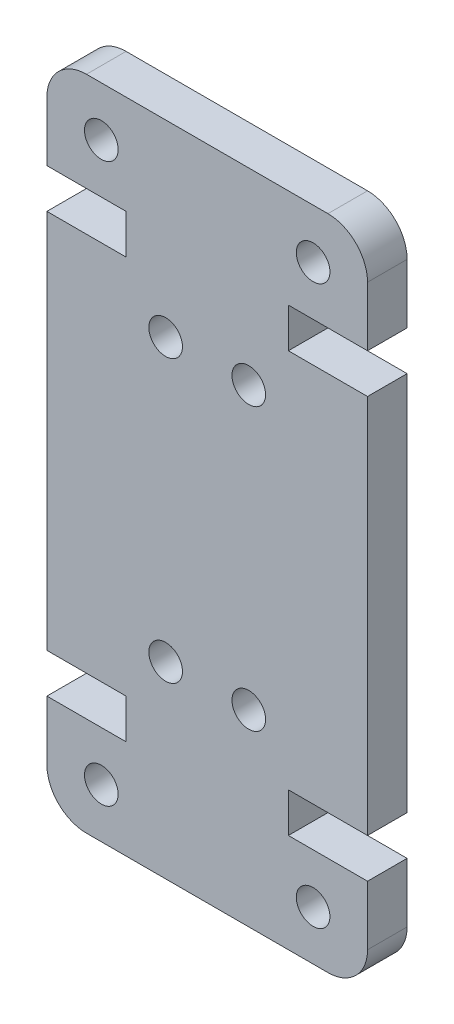
SolidWorks part; units mm, degrees
ref_plane "Front Plane" through (0, 0, 0) normal (0, 0, 1) x (1, 0, 0)
ref_plane "Top Plane" through (0, 0, 0) normal (0, 1, 0) x (1, 0, 0)
ref_plane "Right Plane" through (0, 0, 0) normal (1, 0, 0) x (0, 0, -1)
sketch "Sketch1" plane through (0, 0, 0) normal (0, 0, 1) x (1, 0, 0)
  line L0 (0, 26.21) -> (0, 7)
  line L1 (16.2, 2) -> (16.2, 5)
  line L2 (12.2, 5) -> (16.2, 5)
  line L3 (2, 0) -> (14.2, 0)
  line L4 (16.2, 7) -> (12.2, 7)
  line L5 (12.2, 7) -> (12.2, 5)
  line L6 (16.2, 26.21) -> (16.2, 7)
  line L7 (4, 7) -> (4, 5)
  line L8 (0, 31.21) -> (0, 28.21)
  line L9 (4, 28.21) -> (0, 28.21)
  line L10 (0, 7) -> (4, 7)
  line L11 (0, 26.21) -> (4, 26.21)
  line L12 (4, 5) -> (0, 5)
  line L13 (4, 26.21) -> (4, 28.21)
  line L14 (12.2, 26.21) -> (12.2, 28.21)
  line L15 (16.2, 26.21) -> (12.2, 26.21)
  line L16 (0, 2) -> (0, 5)
  line L17 (2, 33.21) -> (14.2, 33.21)
  line L18 (12.2, 28.21) -> (16.2, 28.21)
  line L19 (16.2, 31.21) -> (16.2, 28.21)
  line L20 (0, 16.605) -> (16.2, 16.605) construction
  line L21 (8.1, 33.21) -> (8.1, 0) construction
  circle A0 centre (13.45, 2.5) radius 0.85
  circle A1 centre (10.2, 9.5) radius 0.85
  arc A2 (16.2, 2) -> (14.2, 0) centre (14.2, 2) cw
  circle A3 centre (2.75, 30.71) radius 0.85
  circle A4 centre (6, 23.71) radius 0.85
  arc A5 (0, 2) -> (2, 0) centre (2, 2) ccw
  arc A6 (0, 31.21) -> (2, 33.21) centre (2, 31.21) cw
  circle A7 centre (6, 9.5) radius 0.85
  arc A8 (16.2, 31.21) -> (14.2, 33.21) centre (14.2, 31.21) ccw
  circle A9 centre (2.75, 2.5) radius 0.85
  circle A10 centre (10.2, 23.71) radius 0.85
  circle A11 centre (13.45, 30.71) radius 0.85
  point P15 (8.1, 16.605)
  dimension "D1" = 1.7
  dimension "D2" = 2
  dimension "D3" = 2.75
  dimension "D4" = 6
  dimension "D5" = 8.1
  dimension "D6" = 2.5
  dimension "D7" = 5
  dimension "D9" = 9.5
  dimension "D10" = 16.605
extrude "Boss-Extrude1" add sketch "Sketch1" along normal blind 4
sketch "Sketch2" plane through (0, 0, 0) normal (0, 0, 1) x (1, 0, 0)
  line L0 (0, 0) -> (16.2, 0)
  line L1 (16.2, 0) -> (16.2, 33.21)
  line L2 (16.2, 33.21) -> (0, 33.21)
  line L3 (0, 33.21) -> (0, 0)
extrude "Cut-Extrude2" cut sketch "Sketch2" along normal blind 2
equation "\"D5@Sketch1\"= \"fingerWidth@parametersSketch@prostheticParameters.SLDPRT\" / 2'PIP width"
equation "\"D10@Sketch1\"= ( \"HL@parametersSketch@prostheticParameters.SLDPRT\" * 0.266 - 12 - 4 ) / 2 'PIP length - Sil. sht PIP-Sil Sht MIP"
equation "\"D1@Sketch1\"= 1.5 + \"tol1@parametersSketch@prostheticParameters.SLDPRT\""
